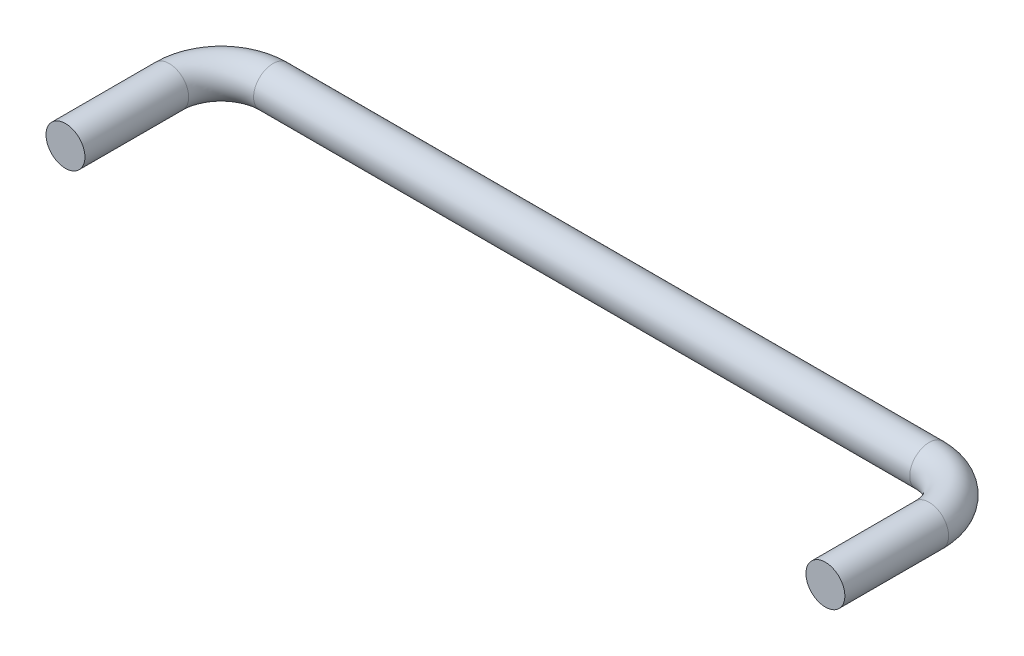
SolidWorks part; units mm, degrees
material "1.4000 (X6Cr13)"
ref_plane "Alzado" through (0, 0, 0) normal (0, 0, 1) x (1, 0, 0)
ref_plane "Planta" through (0, 0, 0) normal (0, 1, 0) x (1, 0, 0)
ref_plane "Vista lateral" through (0, 0, 0) normal (1, 0, 0) x (0, 0, -1)
sketch "Croquis1" plane through (0, 0, 0) normal (0, 1, 0) x (1, 0, 0)
  line L0 (0, 0) -> (0, 20)
  line L1 (10, 30) -> (136.4548, 30)
  line L2 (146.4548, 20) -> (146.4548, 0)
  arc A0 (136.4548, 30) -> (146.4548, 20) centre (136.4548, 20) cw
  arc A1 (10, 30) -> (0, 20) centre (10, 20) ccw
  point P8 (146.4548, 30)
  point P11 (0, 30)
  dimension "D3" = 10
  dimension "D1" = 30
  dimension "D2" = 146.4548
sketch "Croquis2" plane through (0, 0, 0) normal (0, 0, 1) x (1, 0, 0)
  circle A0 centre (0, 0) radius 3.75
  dimension "D1" = 7.5
sweep "Barrer1" add profiles "Croquis2" path "Croquis1"
